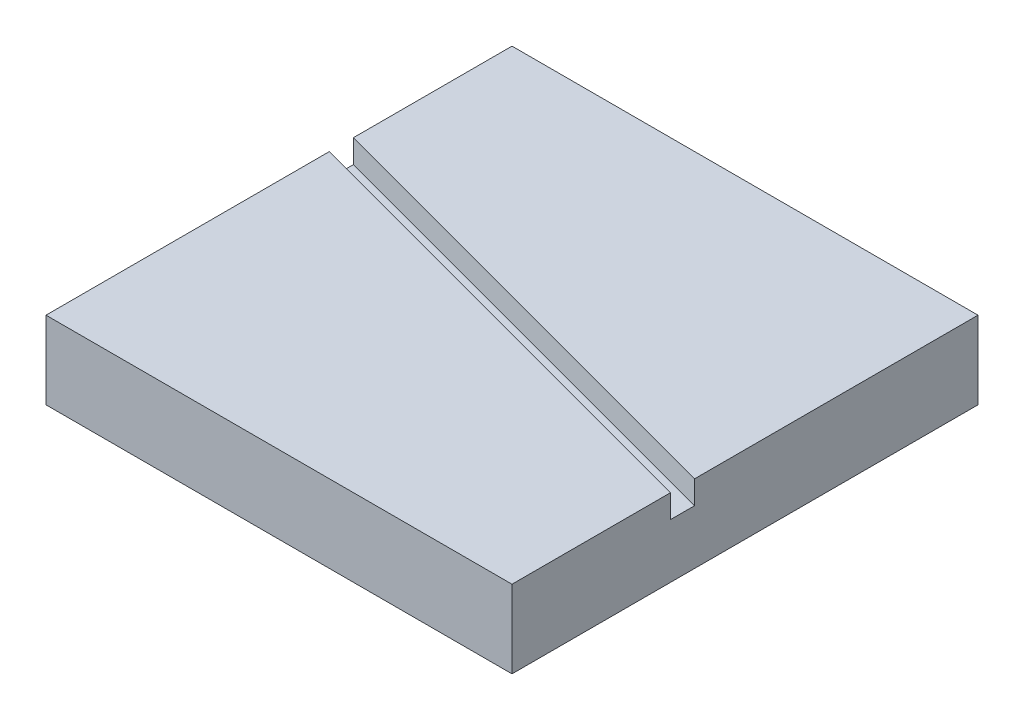
SolidWorks part; units mm, degrees
ref_plane "Front Plane" through (0, 0, 0) normal (0, 0, 1) x (1, 0, 0)
ref_plane "Top Plane" through (0, 0, 0) normal (0, 1, 0) x (1, 0, 0)
ref_plane "Right Plane" through (0, 0, 0) normal (1, 0, 0) x (0, 0, -1)
sketch "Sketch1" plane through (0, 0, 0) normal (0, 1, 0) x (1, 0, 0)
  line L1 (-30, 30) -> (30, 30)
  line L2 (-30, 30) -> (-30, -30)
  line L3 (-30, -30) -> (30, -30)
  line L4 (30, 30) -> (30, -30)
  line L5 (-30, 30) -> (30, -30) construction
  line L6 (-30, -30) -> (30, 30) construction
  point P0 (0, 0)
  dimension "D1" = 60
  dimension "D2" = 60
extrude "Boss-Extrude1" add sketch "Sketch1" along normal blind 10
sketch "Sketch2" plane through (0, 10, 0) normal (0, 1, 0) x (1, 0, 0)
  line L0 (-30, 0) -> (30, 0) construction
  line L1 (-30, 30) -> (-30, -30) construction
  line L2 (30, -30) -> (30, 30) construction
  line L3 (0, 0) -> (30, -8.0385) construction
  line L4 (-34.9823, 7.8206) -> (49.7681, -14.8882)
  line L5 (-34.9823, 7.8206) -> (-34.2059, 10.7184)
  line L6 (49.7681, -14.8882) -> (50.5445, -11.9905)
  line L7 (-34.2059, 10.7184) -> (50.5445, -11.9905)
  line L8 (-34.9823, 7.8206) -> (50.5445, -11.9905) construction
  line L9 (49.7681, -14.8882) -> (-34.2059, 10.7184) construction
  point P9 (7.7811, -2.0849)
  dimension "D1" = 15
  dimension "D2" = 3
extrude "Cut-Extrude1" cut sketch "Sketch2" against normal blind 3
